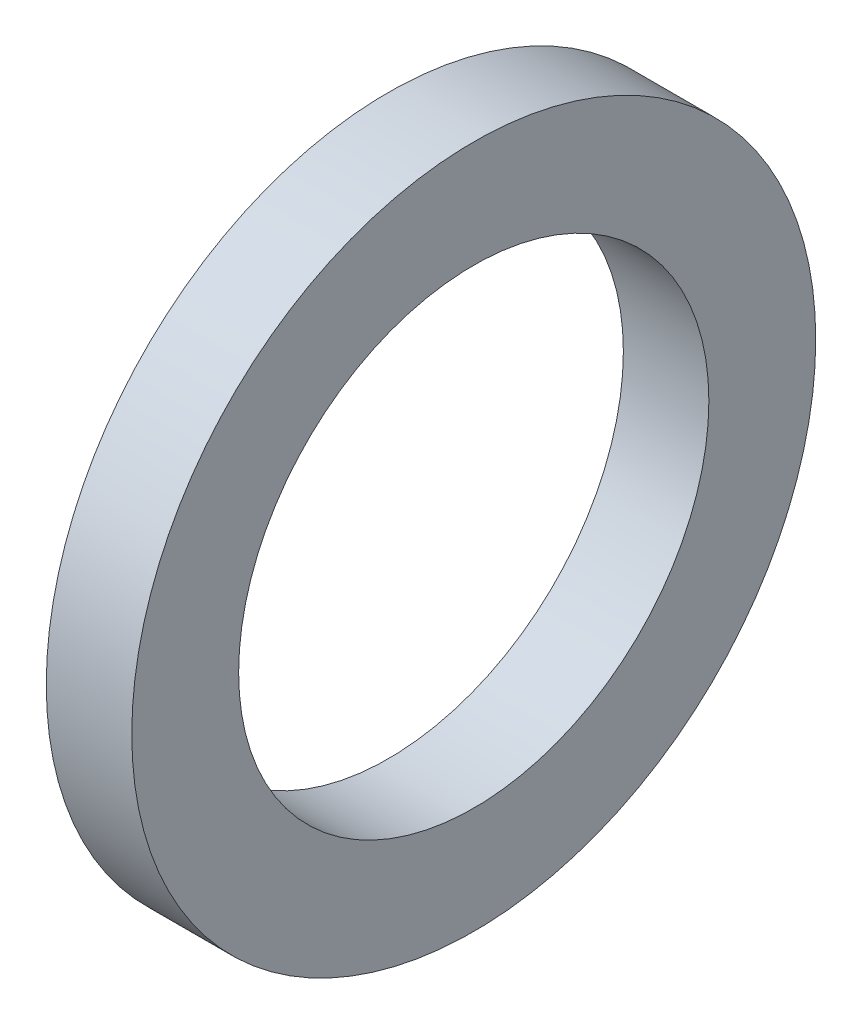
SolidWorks part; units mm, degrees
material "Cobalt"
ref_plane "Front Plane" through (0, 0, 0) normal (0, 0, 1) x (1, 0, 0)
ref_plane "Top Plane" through (0, 0, 0) normal (0, 1, 0) x (1, 0, 0)
ref_plane "Right Plane" through (0, 0, 0) normal (1, 0, 0) x (0, 0, -1)
sketch "Sketch1" plane through (0, 0, 0) normal (0, 0, 1) x (1, 0, 0)
  line L0 (0, 0) -> (0, 25)
  line L1 (0, 25) -> (20, 25)
  line L2 (20, 25) -> (20, 0)
  line L3 (20, 0) -> (0, 0)
  line L4 (0, 0) -> (0.2586, 0.1293)
  line L6 (-87.1403, -55) -> (105.5311, -55) construction
  dimension "D1" = 25
  dimension "D2" = 20
  dimension "D3" = 55
revolve "Revolve1" add sketch "Sketch1" angle 360 about L6
